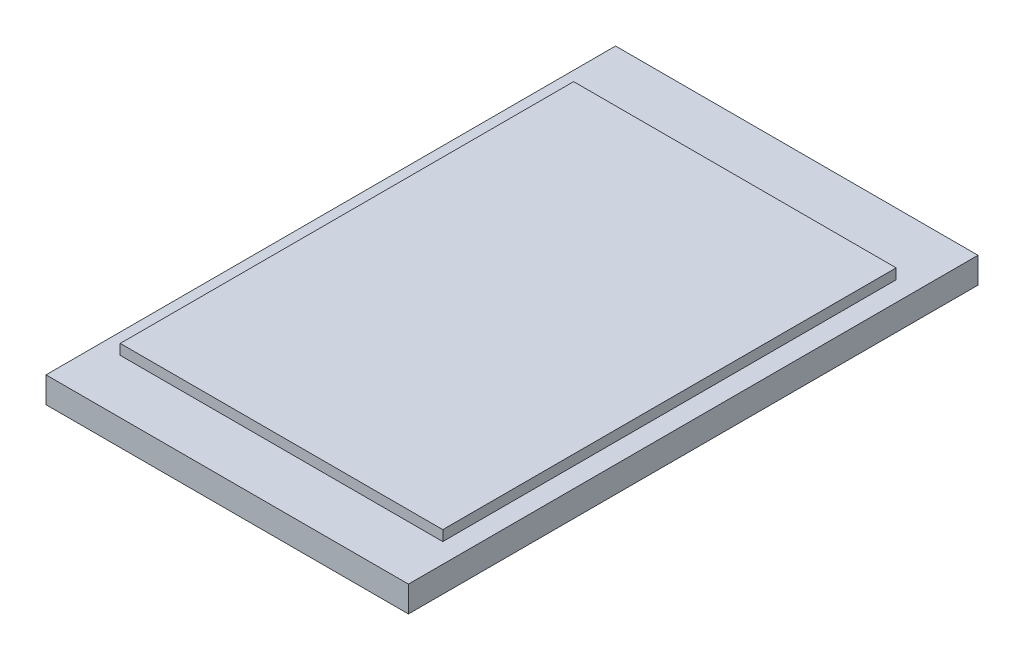
SolidWorks part; units mm, degrees
ref_plane "Front Plane" through (0, 0, 0) normal (0, 0, 1) x (1, 0, 0)
ref_plane "Top Plane" through (0, 0, 0) normal (0, 1, 0) x (1, 0, 0)
ref_plane "Right Plane" through (0, 0, 0) normal (1, 0, 0) x (0, 0, -1)
sketch "Sketch1" plane through (0, 0, 0) normal (0, 1, 0) x (1, 0, 0)
  line L1 (-79.0291, 64.0777) -> (-9.0291, 64.0777)
  line L2 (-79.0291, 64.0777) -> (-79.0291, -45.9223)
  line L3 (-79.0291, -45.9223) -> (-9.0291, -45.9223)
  line L4 (-9.0291, 64.0777) -> (-9.0291, -45.9223)
  dimension "D1" = 110
  dimension "D2" = 70
extrude "Boss-Extrude1" add sketch "Sketch1" along normal blind 5
sketch "Sketch2" plane through (0, 5, 0) normal (0, 1, 0) x (1, 0, 0)
  line L1 (-75.1181, 52.0717) -> (-12.8276, 52.0717)
  line L2 (-75.1181, 52.0717) -> (-75.1181, -35.4962)
  line L3 (-75.1181, -35.4962) -> (-12.8276, -35.4962)
  line L4 (-12.8276, 52.0717) -> (-12.8276, -35.4962)
extrude "Boss-Extrude2" add sketch "Sketch2" along normal blind 2
